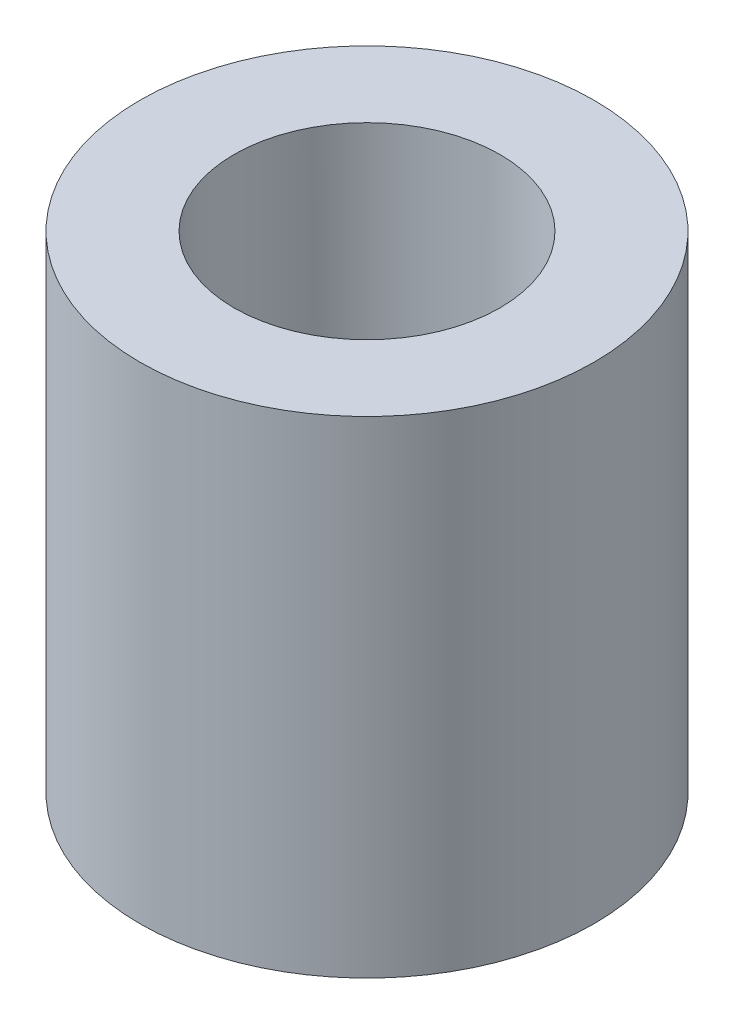
SolidWorks part; units mm, degrees
ref_plane "Спереди" through (0, 0, 0) normal (0, 0, 1) x (1, 0, 0)
ref_plane "Сверху" through (0, 0, 0) normal (0, 1, 0) x (1, 0, 0)
ref_plane "Справа" through (0, 0, 0) normal (1, 0, 0) x (0, 0, -1)
sketch "Sketch1" plane through (0, 0, 0) normal (0, 1, 0) x (1, 0, 0)
  circle A0 centre (0, 0) radius 7
  dimension "D1" = 14
extrude "Boss-Extrude3" add sketch "Sketch1" along normal blind 15
sketch "Sketch4" plane through (0, 15, 0) normal (0, 1, 0) x (1, 0, 0)
  circle A0 centre (0, 0) radius 4.1
  dimension "D1" = 8.2
extrude "Cut-Extrude1" cut sketch "Sketch4" against normal blind 11
sketch "Sketch5" plane through (0, 0, 0) normal (0, -1, 0) x (1, 0, 0)
  line L1 (3.1, 3.1) -> (-3.1, 3.1)
  line L2 (3.1, 3.1) -> (3.1, -3.1)
  line L3 (3.1, -3.1) -> (-3.1, -3.1)
  line L4 (-3.1, 3.1) -> (-3.1, -3.1)
  line L5 (3.1, 3.1) -> (-3.1, -3.1) construction
  line L6 (3.1, -3.1) -> (-3.1, 3.1) construction
  point P0 (0, 0)
  dimension "D1" = 6.2
extrude "Cut-Extrude2" cut sketch "Sketch5" against normal blind 4
